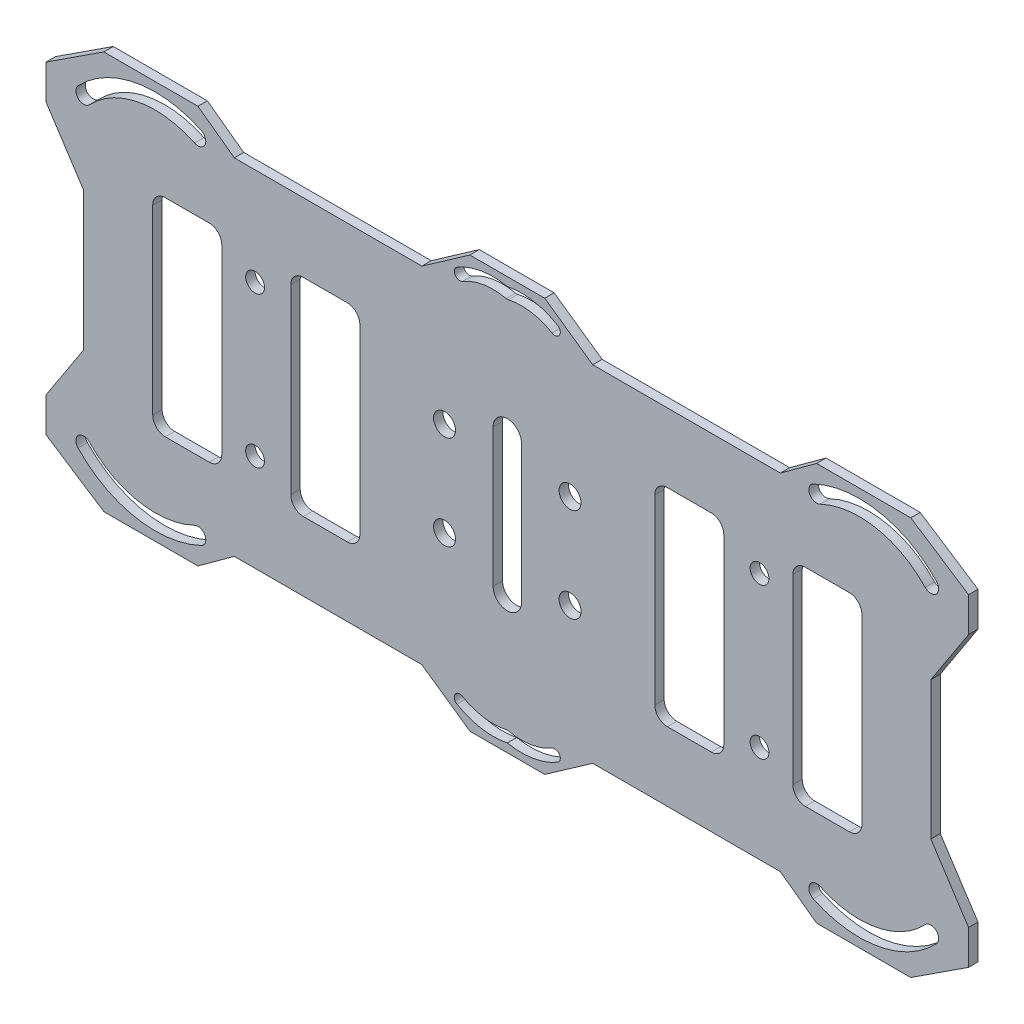
SolidWorks part; units mm, degrees
ref_plane "Piano frontale" through (0, 0, 0) normal (0, 0, 1) x (1, 0, 0)
ref_plane "Piano superiore" through (0, 0, 0) normal (0, 1, 0) x (1, 0, 0)
ref_plane "Piano destro" through (0, 0, 0) normal (1, 0, 0) x (0, 0, -1)
sketch "Schizzo1" plane through (0, 0, 0) normal (0, 0, 1) x (1, 0, 0)
  line L0 (-13.6152, -27.5) -> (-5.9645, -32.8595)
  line L1 (13.6152, -27.5) -> (43.5, -27.5)
  line L2 (-67.5, -11) -> (-67.5, 11)
  line L5 (-67.5, -27.5) -> (67.5, 27.5) construction
  line L6 (-67.5, 27.5) -> (67.5, -27.5) construction
  line L7 (55, 0) -> (-55, 0) construction
  line L8 (-54.5, -16.5) -> (-47.5, -16.5)
  line L9 (-56.5, -14.5) -> (-56.5, 14.5)
  line L11 (-45.5, -14.5) -> (-45.5, 14.5)
  line L12 (-56.5, -16.5) -> (-45.5, 16.5) construction
  line L13 (-56.5, 16.5) -> (-45.5, -16.5) construction
  line L14 (-67.5, -11) -> (-73.5081, -20.2143)
  line L15 (-32.5, -16.5) -> (-25.5, -16.5)
  line L16 (-34.5, -14.5) -> (-34.5, 14.5)
  line L18 (-23.5, -14.5) -> (-23.5, 14.5)
  line L19 (-34.5, -16.5) -> (-23.5, 16.5) construction
  line L20 (-34.5, 16.5) -> (-23.5, -16.5) construction
  line L21 (-73.5081, -20.2143) -> (-73.5081, -25.7143)
  line L22 (-73.5081, -25.7143) -> (-64.2938, -31.7224)
  line L23 (-64.2938, -31.7224) -> (-49.2938, -31.7224)
  line L24 (-49.2938, -31.7224) -> (-43.5, -27.5)
  line L25 (-5.9645, -32.8595) -> (5.9645, -32.8595)
  line L26 (0, -55) -> (0, 55) construction
  line L27 (13.6152, -27.5) -> (5.9645, -32.8595)
  line L29 (45.5, -14.5) -> (45.5, 14.5)
  line L30 (54.5, -16.5) -> (47.5, -16.5)
  line L31 (56.5, -14.5) -> (56.5, 14.5)
  line L33 (23.5, -14.5) -> (23.5, 14.5)
  line L34 (32.5, -16.5) -> (25.5, -16.5)
  line L35 (34.5, -14.5) -> (34.5, 14.5)
  line L36 (49.2938, -31.7224) -> (43.5, -27.5)
  line L37 (64.2938, -31.7224) -> (49.2938, -31.7224)
  line L38 (73.5081, -25.7143) -> (64.2938, -31.7224)
  line L39 (73.5081, -20.2143) -> (73.5081, -25.7143)
  line L40 (67.5, -11) -> (73.5081, -20.2143)
  line L41 (67.5, -11) -> (67.5, 11)
  line L42 (-13.6152, 27.5) -> (-43.5, 27.5)
  line L43 (43.5, -27.5) -> (13.6152, -27.5)
  line L44 (67.5, -11) -> (67.5, 11)
  line L45 (43.5, 27.5) -> (13.6152, 27.5)
  line L46 (-13.6152, -27.5) -> (-43.5, -27.5)
  line L47 (-67.5, -11) -> (-67.5, 11)
  line L48 (67.5, 11) -> (73.5081, 20.2143)
  line L49 (73.5081, 20.2143) -> (73.5081, 25.7143)
  line L50 (73.5081, 25.7143) -> (64.2938, 31.7224)
  line L51 (64.2938, 31.7224) -> (49.2938, 31.7224)
  line L52 (49.2938, 31.7224) -> (43.5, 27.5)
  line L53 (32.5, 16.5) -> (25.5, 16.5)
  line L54 (54.5, 16.5) -> (47.5, 16.5)
  line L55 (13.6152, 27.5) -> (5.9645, 32.8595)
  line L56 (-5.9645, 32.8595) -> (5.9645, 32.8595)
  line L57 (-49.2938, 31.7224) -> (-43.5, 27.5)
  line L58 (-64.2938, 31.7224) -> (-49.2938, 31.7224)
  line L59 (-73.5081, 25.7143) -> (-64.2938, 31.7224)
  line L60 (-73.5081, 20.2143) -> (-73.5081, 25.7143)
  line L61 (-32.5, 16.5) -> (-25.5, 16.5)
  line L62 (-67.5, 11) -> (-73.5081, 20.2143)
  line L63 (-54.5, 16.5) -> (-47.5, 16.5)
  line L64 (13.6152, 27.5) -> (43.5, 27.5)
  line L65 (-13.6152, 27.5) -> (-5.9645, 32.8595)
  line L66 (-67.5, 25.4461) -> (-67.5, 25.8768)
  line L67 (-67.5, 25.4461) -> (-67.5, 25.8768)
  line L68 (0, 11) -> (0, -11) construction
  line L69 (2.2614, 11) -> (2.2614, -11)
  line L70 (-2.2614, 11) -> (-2.2614, -11)
  arc A0 (-25.5, -16.5) -> (-23.5, -14.5) centre (-25.5, -14.5) ccw
  arc A1 (-32.5, -16.5) -> (-34.5, -14.5) centre (-32.5, -14.5) cw
  arc A6 (-47.5, -16.5) -> (-45.5, -14.5) centre (-47.5, -14.5) ccw
  arc A7 (-54.5, -16.5) -> (-56.5, -14.5) centre (-54.5, -14.5) cw
  arc A8 (-67.5, -24.1318) -> (-49.2938, -27.5) centre (-56.089, -13.341) ccw construction
  arc A9 (-68.4056, -24.9882) -> (-48.7545, -28.6237) centre (-56.089, -13.341) ccw
  arc A10 (-66.5944, -23.2754) -> (-49.8331, -26.3763) centre (-56.089, -13.341) ccw
  arc A11 (-66.5944, -23.2754) -> (-68.4056, -24.9882) centre (-67.5, -24.1318) ccw
  arc A12 (-48.7545, -28.6237) -> (-49.8331, -26.3763) centre (-49.2938, -27.5) ccw
  circle A13 centre (-40.1914, -12) radius 1.5
  circle A14 centre (40.1914, 12) radius 1.5
  arc A15 (-8.0181, -30.1482) -> (0.1871, -31.4567) centre (-2.2501, -20.359) ccw
  arc A16 (-7.1323, -28.6449) -> (-0.1871, -29.7524) centre (-2.2501, -20.359) ccw
  arc A17 (-7.1323, -28.6449) -> (-8.0181, -30.1482) centre (-7.5752, -29.3966) ccw
  arc A18 (0.1871, -29.7524) -> (-0.1871, -29.7524) centre (0, -30.6046) ccw
  circle A19 centre (40.1914, -12) radius 1.5
  arc A20 (8.0181, -30.1482) -> (-0.1871, -31.4567) centre (2.2501, -20.359) cw
  arc A21 (7.1323, -28.6449) -> (0.1871, -29.7524) centre (2.2501, -20.359) cw
  arc A22 (7.1323, -28.6449) -> (8.0181, -30.1482) centre (7.5752, -29.3966) cw
  arc A23 (-0.1871, -29.7524) -> (0.1871, -29.7524) centre (0, -30.6046) cw
  arc A25 (47.5, -16.5) -> (45.5, -14.5) centre (47.5, -14.5) cw
  arc A27 (54.5, -16.5) -> (56.5, -14.5) centre (54.5, -14.5) ccw
  arc A29 (25.5, -16.5) -> (23.5, -14.5) centre (25.5, -14.5) cw
  arc A30 (32.5, -16.5) -> (34.5, -14.5) centre (32.5, -14.5) ccw
  arc A32 (67.5, -24.1318) -> (49.2938, -27.5) centre (56.089, -13.341) cw construction
  arc A33 (68.4056, -24.9882) -> (48.7545, -28.6237) centre (56.089, -13.341) cw
  arc A34 (66.5944, -23.2754) -> (49.8331, -26.3763) centre (56.089, -13.341) cw
  arc A35 (66.5944, -23.2754) -> (68.4056, -24.9882) centre (67.5, -24.1318) cw
  arc A36 (48.7545, -28.6237) -> (49.8331, -26.3763) centre (49.2938, -27.5) cw
  arc A37 (-67.5, 24.1318) -> (-49.2938, 27.5) centre (-56.089, 13.341) cw construction
  arc A38 (-68.4056, 24.9882) -> (-48.7545, 28.6237) centre (-56.089, 13.341) cw
  arc A39 (-66.5944, 23.2754) -> (-49.8331, 26.3763) centre (-56.089, 13.341) cw
  arc A40 (-66.5944, 23.2754) -> (-68.4056, 24.9882) centre (-67.5, 24.1318) cw
  arc A41 (-48.7545, 28.6237) -> (-49.8331, 26.3763) centre (-49.2938, 27.5) cw
  arc A42 (67.5, 24.1318) -> (49.2938, 27.5) centre (56.089, 13.341) ccw construction
  arc A43 (68.4056, 24.9882) -> (48.7545, 28.6237) centre (56.089, 13.341) ccw
  arc A44 (66.5944, 23.2754) -> (49.8331, 26.3763) centre (56.089, 13.341) ccw
  arc A45 (66.5944, 23.2754) -> (68.4056, 24.9882) centre (67.5, 24.1318) ccw
  arc A46 (48.7545, 28.6237) -> (49.8331, 26.3763) centre (49.2938, 27.5) ccw
  arc A47 (2.2614, 11) -> (-2.2614, 11) centre (0, 11) ccw
  arc A48 (-2.2614, -11) -> (2.2614, -11) centre (0, -11) ccw
  arc A49 (32.5, 16.5) -> (34.5, 14.5) centre (32.5, 14.5) cw
  arc A50 (25.5, 16.5) -> (23.5, 14.5) centre (25.5, 14.5) ccw
  arc A51 (54.5, 16.5) -> (56.5, 14.5) centre (54.5, 14.5) cw
  arc A52 (47.5, 16.5) -> (45.5, 14.5) centre (47.5, 14.5) ccw
  arc A53 (-0.1871, 29.7524) -> (0.1871, 29.7524) centre (0, 30.6046) ccw
  arc A54 (7.1323, 28.6449) -> (8.0181, 30.1482) centre (7.5752, 29.3966) ccw
  arc A55 (7.1323, 28.6449) -> (0.1871, 29.7524) centre (2.2501, 20.359) ccw
  arc A56 (8.0181, 30.1482) -> (-0.1871, 31.4567) centre (2.2501, 20.359) ccw
  arc A57 (0.1871, 29.7524) -> (-0.1871, 29.7524) centre (0, 30.6046) cw
  arc A58 (-7.1323, 28.6449) -> (-8.0181, 30.1482) centre (-7.5752, 29.3966) cw
  arc A59 (-7.1323, 28.6449) -> (-0.1871, 29.7524) centre (-2.2501, 20.359) cw
  arc A60 (-8.0181, 30.1482) -> (0.1871, 31.4567) centre (-2.2501, 20.359) cw
  circle A61 centre (-40.1914, 12) radius 1.5
  arc A62 (-54.5, 16.5) -> (-56.5, 14.5) centre (-54.5, 14.5) ccw
  arc A63 (-47.5, 16.5) -> (-45.5, 14.5) centre (-47.5, 14.5) cw
  arc A64 (-32.5, 16.5) -> (-34.5, 14.5) centre (-32.5, 14.5) ccw
  arc A65 (-25.5, 16.5) -> (-23.5, 14.5) centre (-25.5, 14.5) cw
  point P0 (0, 0)
  point P6 (-51, 0)
  point P13 (-29, 0)
  point P29 (-58.946, 28.7841)
  point P51 (-58.946, -28.7841)
  point P66 (-3.902, -30.7178)
  point P72 (0, -32.8595)
  point P76 (3.902, -30.7178)
  point P89 (58.946, 28.7841)
  point P108 (58.946, -28.7841)
  point P166 (3.902, 30.7178)
  point P167 (0, 32.8595)
  point P168 (-3.902, 30.7178)
  point P176 (0, 0)
  dimension "D8" = 2
  dimension "D15" = 3
  dimension "D1" = 135
  dimension "D2" = 55
  dimension "D3" = 16.5
  dimension "D4" = 11
  dimension "D5" = 38.5
  dimension "D6" = 11
  dimension "D7" = 33
  dimension "D9" = 11
  dimension "D10" = 11
  dimension "D11" = 5.5
  dimension "D12" = 11
  dimension "D13" = 15
  dimension "D14" = 24
  dimension "D16" = 12
extrude "Estrusione-Estrusione1" add sketch "Schizzo1" along normal mid plane 1.5 contours L65 L42 L57 L58 L59 L60 L62 L2 L14 L21 L22 L23 L24 L46 L0 L25 L27 L1 L36 L37 L38 L39 L40 L41 L48 L49 L50 L51 L52 L45 L55 L56 A58 A60 A56 A54 A55 A53 A59 A38 A41 A39 A40 A33 A36 A34 A35
sketch "Sketch1" plane through (0, 0, -0.75) normal (0, 0, -1) x (-1, 0, 0)
  line L0 (0, 0.825) -> (0, -0.825) construction
  line L1 (0.825, 0) -> (-0.825, 0) construction
  circle A0 centre (-10, 7.5) radius 1.75
  circle A1 centre (-10, -7.5) radius 1.75
  circle A2 centre (10, -7.5) radius 1.75
  circle A3 centre (10, 7.5) radius 1.75
  dimension "D1" = 10
  dimension "D2" = 7.5
extrude "Cut-Extrude1" cut sketch "Sketch1" against normal through all both and the other way through all
ref_point "Point1"
